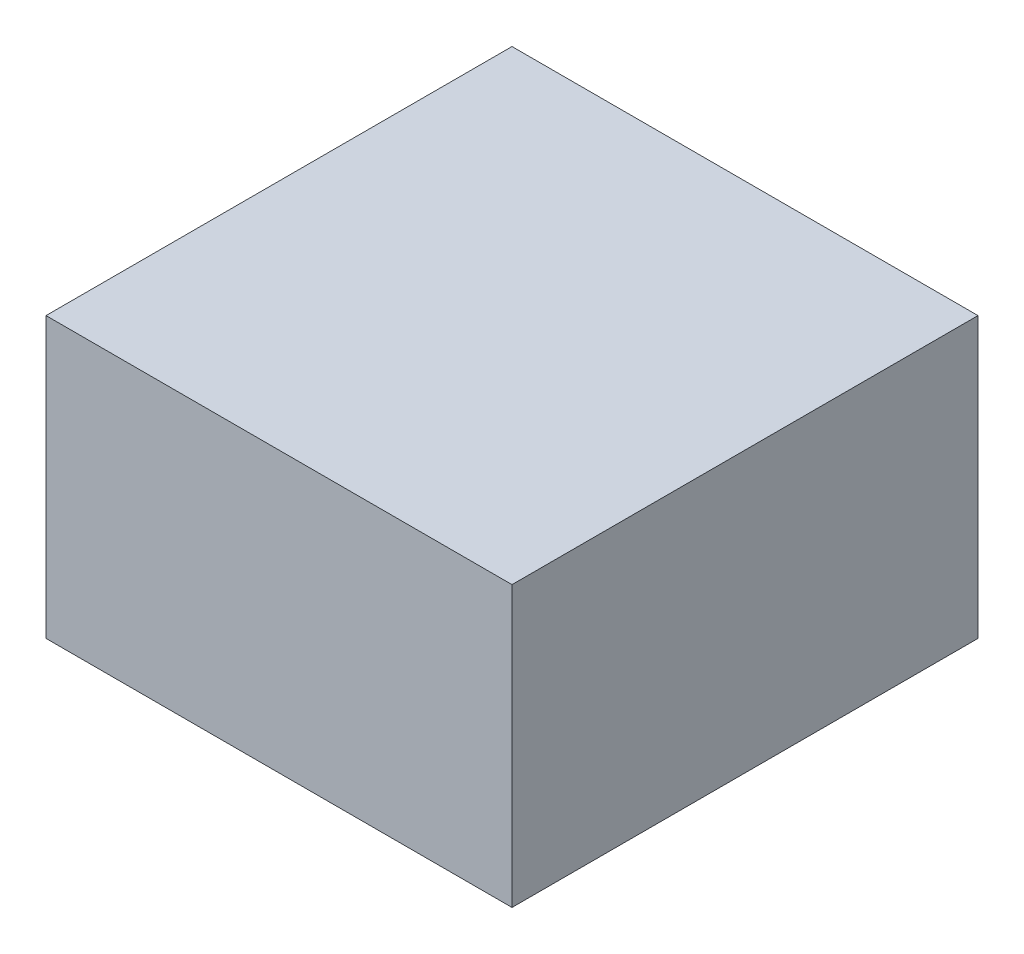
SolidWorks part; units mm, degrees
ref_plane "Front Plane" through (0, 0, 0) normal (0, 0, 1) x (1, 0, 0)
ref_plane "Top Plane" through (0, 0, 0) normal (0, 1, 0) x (1, 0, 0)
ref_plane "Right Plane" through (0, 0, 0) normal (1, 0, 0) x (0, 0, -1)
sketch "Эскиз1" plane through (0, 0, 0) normal (0, 0, 1) x (1, 0, 0)
  line L1 (-25, -15) -> (25, -15)
  line L2 (-25, -15) -> (-25, 15)
  line L3 (-25, 15) -> (25, 15)
  line L4 (25, -15) -> (25, 15)
  line L5 (-25, -15) -> (25, 15) construction
  line L6 (-25, 15) -> (25, -15) construction
  point P0 (0, 0)
  dimension "D1" = 30
  dimension "D2" = 50
extrude "Бобышка-Вытянуть1" add sketch "Эскиз1" along normal mid plane 50
